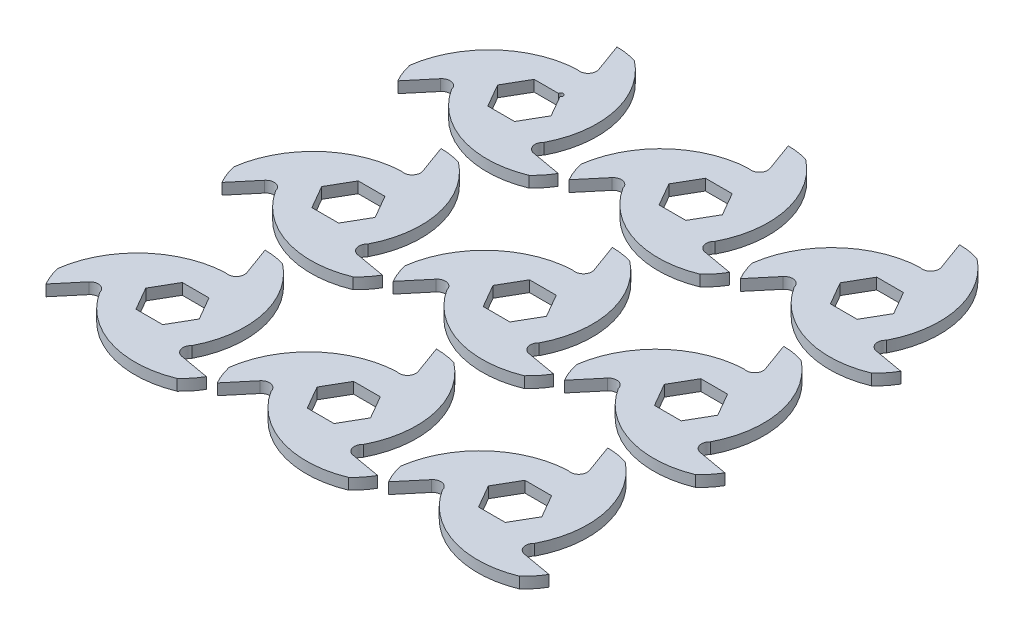
SolidWorks part; units mm, degrees
ref_plane "Front Plane" through (0, 0, 0) normal (0, 0, 1) x (1, 0, 0)
ref_plane "Top Plane" through (0, 0, 0) normal (0, 1, 0) x (1, 0, 0)
ref_plane "Right Plane" through (0, 0, 0) normal (1, 0, 0) x (0, 0, -1)
sketch "Sketch2" plane through (0, 0, 0) normal (0, 1, 0) x (1, 0, 0)
  line L0 (0, 50.8) -> (0, 0) construction
  line L1 (0, 0) -> (-43.9941, -25.4) construction
  line L2 (0, 0) -> (43.9941, -25.4) construction
  line L3 (0, 50.8) -> (5.6992, 35.1416)
  line L4 (43.9941, -25.4) -> (27.5839, -22.5064)
  line L5 (-43.9941, -25.4) -> (-33.2831, -12.6352)
  line L7 (7.3323, 12.7) -> (-7.3323, 12.7)
  line L8 (-7.3323, 12.7) -> (-14.6647, 0)
  line L9 (-14.6647, 0) -> (-7.3323, -12.7)
  line L10 (-7.3323, -12.7) -> (7.3323, -12.7)
  line L11 (7.3323, -12.7) -> (14.6647, 0)
  line L12 (14.6647, 0) -> (7.3323, 12.7)
  circle A0 centre (0, 0) radius 50.8 construction
  circle A1 centre (0, 13.2055) radius 37.5945
  circle A2 centre (11.4363, -6.6028) radius 37.5945
  circle A3 centre (-11.4363, -6.6028) radius 37.5945
  arc A4 (5.6992, 35.1416) -> (0, 29.21) centre (1.3938, 33.5746) cw
  arc A5 (27.5839, -22.5064) -> (25.2966, -14.605) centre (28.3796, -17.9943) cw
  arc A6 (-33.2831, -12.6352) -> (-25.2966, -14.605) centre (-29.7733, -15.5803) cw
  circle A7 centre (0, 0) radius 12.7 construction
  point P25 (0, 0)
  dimension "D1" = 101.6
  dimension "D4" = 20
  dimension "D6" = 30
  dimension "D2" = 120
  dimension "D3" = 120
  dimension "D5" = 21.59
  dimension "D8" = 25.4
  dimension "D7" = 3
extrude "Boss-Extrude2" add sketch "Sketch2" along normal mid plane 6.096 contours A1 A3 A2 L12 L11 L10 L9 L8 L7 | A1 A6 A2 A3 | L5 A6 A1 A3 | L4 A5 A3 A2 | A3 A5 A1 A2 | A2 A4 A3 A1 | L3 A4 A2 A1
sketch "Sketch3" plane through (0, 3.048, 0) normal (0, 1, 0) x (1, 0, 0)
  line L3 (43.9941, -25.4) -> (27.5839, -22.5064)
  line L4 (0, 50.8) -> (5.6992, 35.1416)
  line L5 (-43.9941, -25.4) -> (-33.2831, -12.6352)
  line L6 (43.9941, -25.4) -> (27.5839, -22.5064)
  line L7 (0, 50.8) -> (5.6992, 35.1416)
  line L8 (-43.9941, -25.4) -> (-33.2831, -12.6352)
  arc A0 (-48.1379, -14.7476) -> (0, 29.21) centre (2.2057, -21.5421) cw
  arc A1 (0, 29.21) -> (-43.9941, -25.4) centre (-11.4363, -6.6028) ccw construction
  arc A2 (0, 29.21) -> (5.6992, 35.1416) centre (1.3938, 33.5746) ccw construction
  arc A3 (11.2972, 49.0624) -> (25.2966, -14.605) centre (-19.7588, 8.8609) cw
  arc A4 (36.8407, -34.3148) -> (-25.2966, -14.605) centre (17.5532, 12.6812) cw
  arc A9 (-25.2966, -14.605) -> (-33.2831, -12.6352) centre (-29.7733, -15.5803) ccw
  arc A10 (-25.2966, -14.605) -> (43.9941, -25.4) centre (11.4363, -6.6028) ccw
  arc A11 (25.2966, -14.605) -> (27.5839, -22.5064) centre (28.3796, -17.9943) ccw
  arc A12 (25.2966, -14.605) -> (0, 50.8) centre (0, 13.2055) ccw
  arc A13 (0, 29.21) -> (5.6992, 35.1416) centre (1.3938, 33.5746) ccw
  arc A14 (0, 29.21) -> (-43.9941, -25.4) centre (-11.4363, -6.6028) ccw
  arc A15 (-25.2966, -14.605) -> (-33.2831, -12.6352) centre (-29.7733, -15.5803) ccw
  arc A16 (-25.2966, -14.605) -> (43.9941, -25.4) centre (11.4363, -6.6028) ccw
  arc A17 (25.2966, -14.605) -> (27.5839, -22.5064) centre (28.3796, -17.9943) ccw
  arc A18 (25.2966, -14.605) -> (0, 50.8) centre (0, 13.2055) ccw
  arc A19 (0, 29.21) -> (5.6992, 35.1416) centre (1.3938, 33.5746) ccw
  arc A20 (0, 29.21) -> (-43.9941, -25.4) centre (-11.4363, -6.6028) ccw
  point P26 (0, 0)
  arc M20 (-25.2966, -14.605) -> (43.9941, -25.4) centre (11.4363, -6.6028) ccw
  arc M23 (25.2966, -14.605) -> (0, 50.8) centre (0, 13.2055) ccw
  arc M26 (0, 29.21) -> (-43.9941, -25.4) centre (-11.4363, -6.6028) ccw
  dimension "D3" = 50.8
  dimension "D1" = 11.43
  dimension "D2" = 0
  dimension "D4" = 3
extrude "Cut-Extrude1" cut sketch "Sketch3" against normal through all contours A0 M26 | A3 M23 | A4 M20
pattern_linear "LPattern1" count 3 spacing 96.52 along (0, 0, 1) count 3 spacing 93.98 along (1, 0, 0) of "Boss-Extrude2"
sketch "Sketch4" plane through (0, 3.048, 0) normal (0, 1, 0) x (1, 0, 0)
  circle A0 centre (7.3323, 12.7) radius 1.27
  dimension "D1" = 2.54
extrude "Cut-Extrude2" cut sketch "Sketch4" against normal through all
